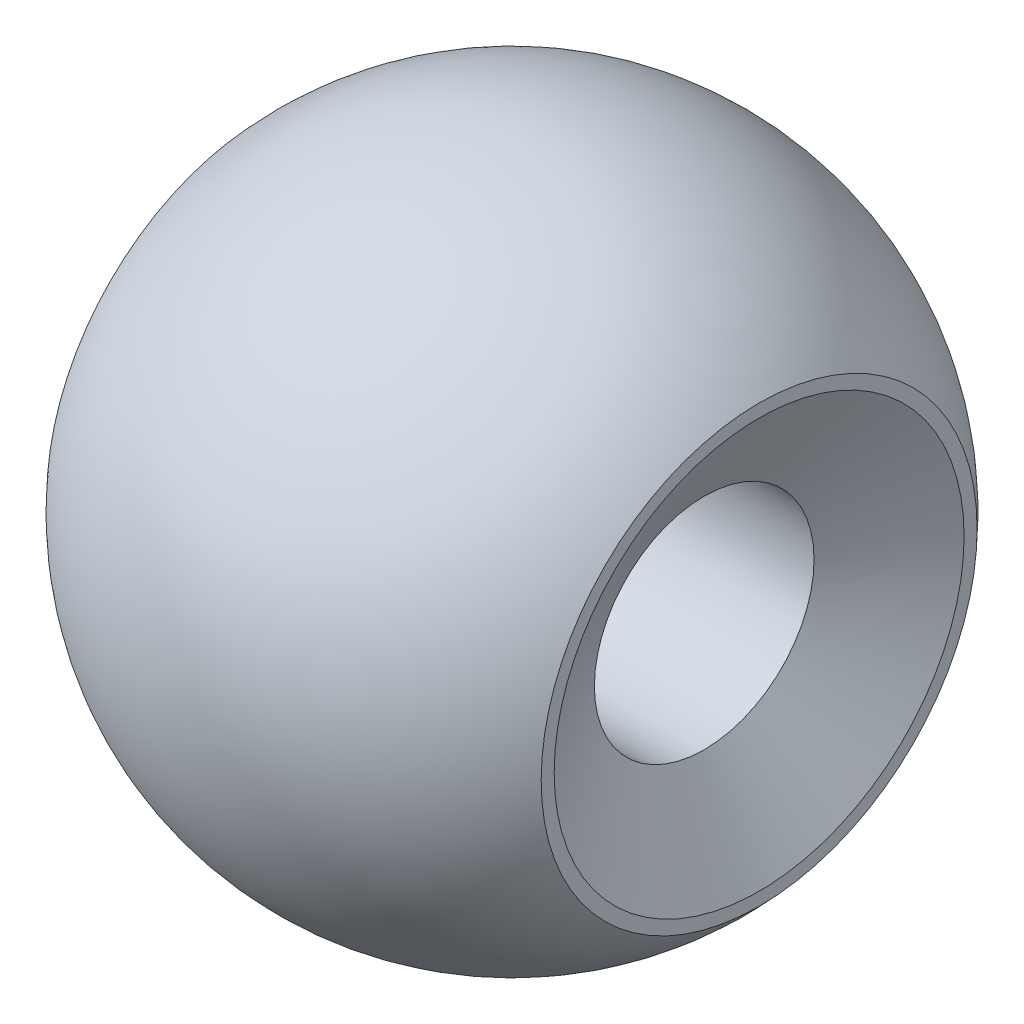
SolidWorks part; units mm, degrees
ref_plane "Front Plane" through (0, 0, 0) normal (0, 0, 1) x (1, 0, 0)
ref_plane "Top Plane" through (0, 0, 0) normal (0, 1, 0) x (1, 0, 0)
ref_plane "Right Plane" through (0, 0, 0) normal (1, 0, 0) x (0, 0, -1)
sketch "Sketch2" plane through (0, 0, 0) normal (0, 1, 0) x (1, 0, 0)
  line L0 (0, 6) -> (0, -6)
  arc A0 (0, 6) -> (0, -6) centre (0, 0) ccw
revolve "Revolve10" add sketch "Sketch2" angle 360 about L0
sketch "Sketch3" plane through (0, 0, 0) normal (0, 1, 0) x (1, 0, 0)
  line L0 (-4.5, 6.1166) -> (-8.0399, -0.6191)
  line L2 (4.5, -6.1166) -> (4.5, 6.1166)
  line L4 (-4.5, -6.1166) -> (-4.5, 6.1166)
  line L7 (-8.0399, -0.6191) -> (-4.5, -6.1166)
  line L8 (4.5, 6.1166) -> (7.1154, -1.2299)
  line L9 (7.1154, -1.2299) -> (4.5, -6.1166)
  point P0 (0, 0)
  dimension "D1" = 9
extrude "Cut-Extrude1" cut sketch "Sketch3" against normal mid plane 20
sketch "Sketch4" plane through (4.5, 0, 0) normal (1, 0, 0) x (0, 0, -1)
  circle A0 centre (0, 0) radius 2
extrude "Cut-Extrude2" cut sketch "Sketch4" against normal up to next
chamfer "Chamfer1" distance 1 angle 60 1 edges at (4.5, 0, -2)
